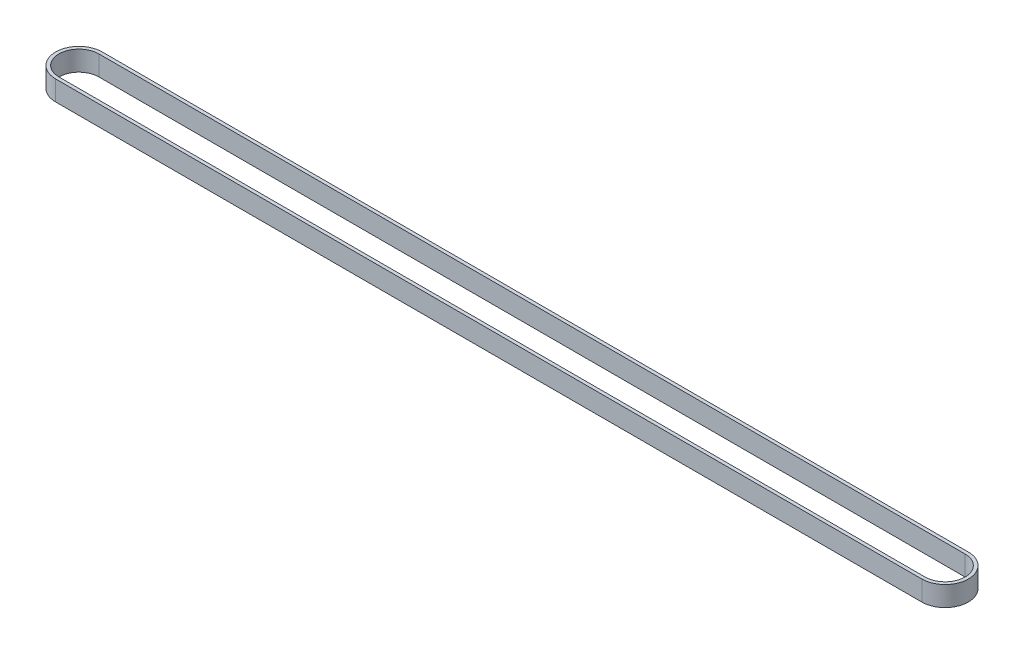
SolidWorks part; units mm, degrees
material "BUTYL"
ref_plane "Front Plane" through (0, 0, 0) normal (0, 0, 1) x (1, 0, 0)
ref_plane "Top Plane" through (0, 0, 0) normal (0, 1, 0) x (1, 0, 0)
ref_plane "Right Plane" through (0, 0, 0) normal (1, 0, 0) x (0, 0, -1)
sketch "Sketch1" plane through (0, 0, 0) normal (0, 1, 0) x (1, 0, 0)
  line L0 (0, 0) -> (260, 0) construction
  line L1 (0, 6) -> (260, 6)
  line L2 (0, -6) -> (260, -6)
  line L3 (0, 0) -> (260, 0) construction
  line L4 (0, 7) -> (260, 7)
  line L5 (0, -7) -> (260, -7)
  arc A0 (0, 6) -> (0, -6) centre (0, 0) ccw
  arc A1 (260, -6) -> (260, 6) centre (260, 0) ccw
  arc A2 (0, 7) -> (0, -7) centre (0, 0) ccw
  arc A3 (260, -7) -> (260, 7) centre (260, 0) ccw
  point P3 (130, 0)
  point P10 (130, 0)
  dimension "D2" = 6
  dimension "D3" = 1
  dimension "D1" = 260
extrude "Boss-Extrude1" add sketch "Sketch1" along normal blind 6
